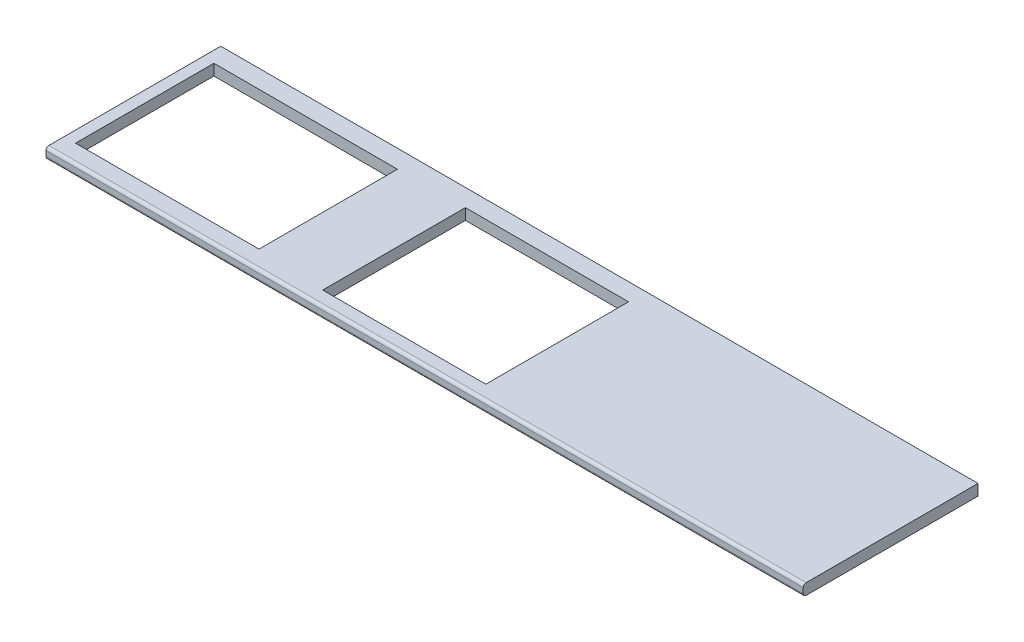
SolidWorks part; units mm, degrees
ref_plane "Спереди" through (0, 0, 0) normal (0, 0, 1) x (1, 0, 0)
ref_plane "Сверху" through (0, 0, 0) normal (0, 1, 0) x (1, 0, 0)
ref_plane "Справа" through (0, 0, 0) normal (1, 0, 0) x (0, 0, -1)
sketch "Эскиз1" plane through (0, 0, 0) normal (0, 1, 0) x (1, 0, 0)
  line L1 (1300, -300) -> (-1300, -300)
  line L2 (1300, -300) -> (1300, 300)
  line L3 (1300, 300) -> (-1300, 300)
  line L4 (-1300, -300) -> (-1300, 300)
  line L5 (1300, -300) -> (-1300, 300) construction
  line L6 (1300, 300) -> (-1300, -300) construction
  point P0 (0, 0)
  dimension "D1" = 600
  dimension "D2" = 2600
extrude "Бобышка-Вытянуть1" add sketch "Эскиз1" along normal blind 38
fillet "Скругление1" radius 10 2 edges at (0, 38, 300) (0, 0, 300)
sketch "Эскиз2" plane through (0, 38, 0) normal (0, 1, 0) x (1, 0, 0)
  line L0 (1300, 300) -> (-1300, 300) construction
  line L1 (-400, 240) -> (160, 240)
  line L2 (-400, 240) -> (-400, -250)
  line L3 (-400, -250) -> (160, -250)
  line L4 (160, 240) -> (160, -250)
  line L5 (-400, 240) -> (160, -250) construction
  line L6 (-400, -250) -> (160, 240) construction
  line L7 (-1300, 300) -> (-1300, -290) construction
  line L8 (1300, -300) -> (-1300, -300) construction
  line L9 (-1261, -300) -> (-1261, -237.5) construction
  line L10 (-1261, 237.5) -> (-631, 237.5)
  line L11 (-1261, 237.5) -> (-1261, -237.5)
  line L12 (-1261, -237.5) -> (-631, -237.5)
  line L13 (-631, 237.5) -> (-631, -237.5)
  line L14 (-1261, 237.5) -> (-631, -237.5) construction
  line L15 (-1261, -237.5) -> (-631, 237.5) construction
  line L16 (-1261, 237.5) -> (-1261, 300) construction
  point P0 (-120, -5)
  point P11 (-946, 0)
  dimension "D1" = 560
  dimension "D2" = 490
  dimension "D3" = 60
  dimension "D4" = 900
  dimension "D5" = 50
  dimension "D6" = 475
  dimension "D7" = 630
  dimension "D8" = 39
  dimension "D9" = 231
extrude "Вырез-Вытянуть1" cut sketch "Эскиз2" against normal through all both and the other way through all
